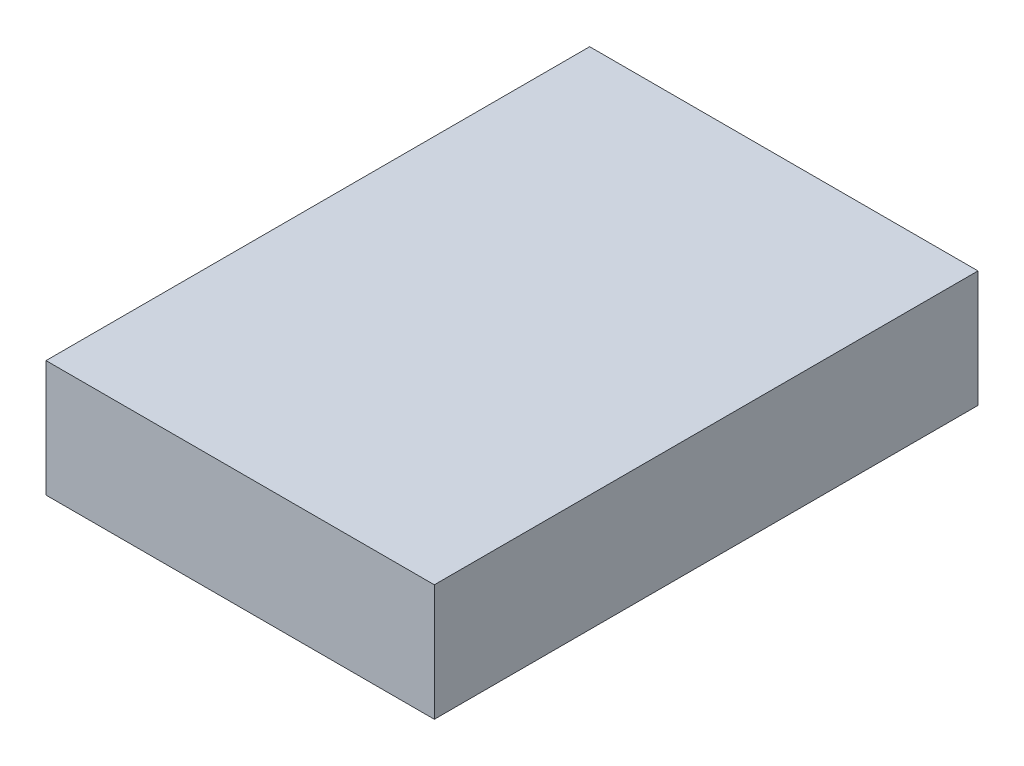
SolidWorks part; units mm, degrees
ref_plane "Front Plane" through (0, 0, 0) normal (0, 0, 1) x (1, 0, 0)
ref_plane "Top Plane" through (0, 0, 0) normal (0, 1, 0) x (1, 0, 0)
ref_plane "Right Plane" through (0, 0, 0) normal (1, 0, 0) x (0, 0, -1)
sketch "Sketch1" plane through (0, 0, 0) normal (0, 1, 0) x (1, 0, 0)
  line L1 (-69.4972, 30.8681) -> (-5.9972, 30.8681)
  line L2 (-69.4972, 30.8681) -> (-69.4972, -58.0319)
  line L3 (-69.4972, -58.0319) -> (-5.9972, -58.0319)
  line L4 (-5.9972, 30.8681) -> (-5.9972, -58.0319)
  dimension "D1" = 88.9
  dimension "D2" = 63.5
extrude "Boss-Extrude1" add sketch "Sketch1" along normal blind 19.05
